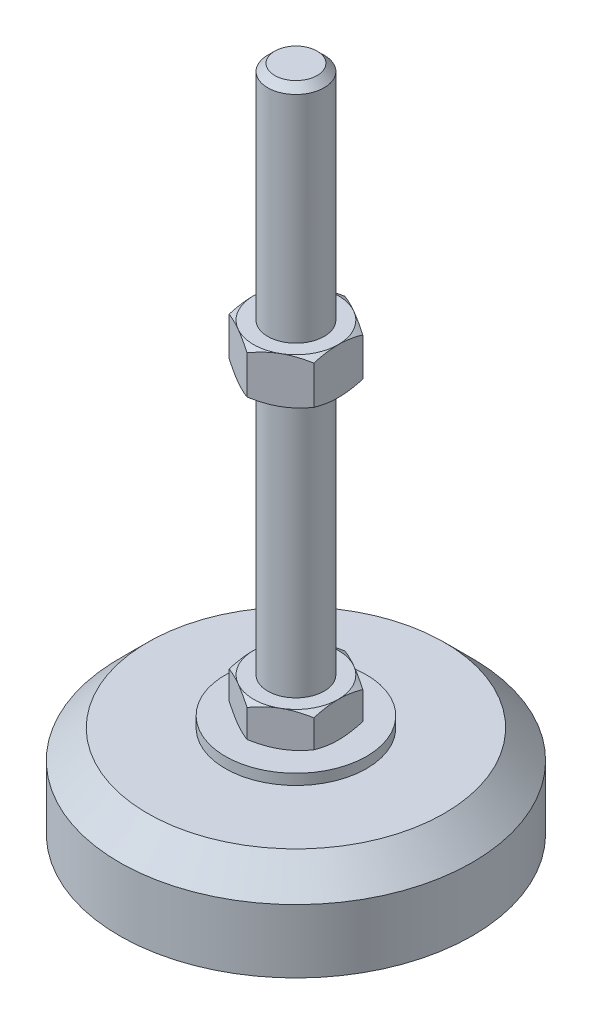
SolidWorks part; units mm, degrees
ref_plane "Спереди" through (0, 0, 0) normal (0, 0, 1) x (1, 0, 0)
ref_plane "Сверху" through (0, 0, 0) normal (0, 1, 0) x (1, 0, 0)
ref_plane "Справа" through (0, 0, 0) normal (1, 0, 0) x (0, 0, -1)
sketch "Эскиз1" plane through (0, 0, 0) normal (0, 0, 1) x (1, 0, 0)
  line L0 (0, 0) -> (-50, 0)
  line L3 (-50, 0) -> (-50, 18)
  line L5 (-20, 29) -> (-8, 29)
  line L12 (-8, 39) -> (-8, 187)
  line L13 (-8, 187) -> (-6, 189)
  line L14 (-6, 189) -> (0, 189)
  line L15 (0, 189) -> (0, 0) construction
  line L16 (-8, 29) -> (0, 29) construction
  line L17 (0, 0) -> (0, 189)
  line L18 (0, 0) -> (0, -7.9595) construction
  line L19 (-8, 39) -> (-8, 29)
  line L20 (-20, 29) -> (-20, 26)
  line L21 (-20, 26) -> (-42, 26)
  line L22 (-42, 26) -> (-50, 18)
  point P8 (-8, 113)
  point P23 (-14, 29)
  dimension "D1" = 16
  dimension "D2" = 29
  dimension "D3" = 10
  dimension "D4" = 100
  dimension "D5" = 8
  dimension "D6" = 2
  dimension "D7" = 45
  dimension "D8" = 40
  dimension "D10" = 150
  dimension "D11" = 18
  dimension "D12" = 45
  dimension "D13" = 3
revolve "Повернуть1" add sketch "Эскиз1" angle 360 about L17
sketch "Эскиз2" plane through (0, 29, 0) normal (0, 1, 0) x (1, 0, 0)
  line L1 (0, 13.8564) -> (-12, 6.9282)
  line L2 (-12, 6.9282) -> (-12, -6.9282)
  line L3 (-12, -6.9282) -> (0, -13.8564)
  line L4 (0, -13.8564) -> (12, -6.9282)
  line L5 (12, -6.9282) -> (12, 6.9282)
  line L6 (12, 6.9282) -> (0, 13.8564)
  circle A0 centre (0, 0) radius 12 construction
  dimension "D1" = 24
extrude "Бобышка-Вытянуть1" add sketch "Эскиз2" along normal up to vertex (10 mm away) up to point (-8, 39, 0)
ref_plane "Плоскость1" through (0, 113, 0) normal (0, 1, 0) x (1, 0, 0)
sketch "Эскиз3" plane through (0, 113, 0) normal (0, 1, 0) x (1, 0, 0)
  line L6 (12, 6.9282) -> (0, 13.8564)
  line L7 (0, 13.8564) -> (-12, 6.9282)
  line L8 (-12, 6.9282) -> (-12, -6.9282)
  line L9 (-12, -6.9282) -> (0, -13.8564)
  line L10 (0, -13.8564) -> (12, -6.9282)
  line L11 (12, -6.9282) -> (12, 6.9282)
  line L12 (12, 6.9282) -> (0, 13.8564)
  line L13 (0, 13.8564) -> (-12, 6.9282)
  line L14 (-12, 6.9282) -> (-12, -6.9282)
  line L15 (-12, -6.9282) -> (0, -13.8564)
  line L16 (0, -13.8564) -> (12, -6.9282)
  line L17 (12, -6.9282) -> (12, 6.9282)
  dimension "D1" = 0
extrude "Бобышка-Вытянуть2" add sketch "Эскиз3" along normal blind 13
sketch "Эскиз4" plane through (0, 0, 0) normal (0, 0, 1) x (1, 0, 0)
  line L0 (-12, 126) -> (-23.2583, 119.5)
  line L1 (-23.2583, 119.5) -> (-23.2583, 126)
  line L2 (-23.2583, 126) -> (-12, 126)
  line L3 (-23.2583, 119.5) -> (-12, 113)
  line L4 (50, 113) -> (-50, 113) construction
  line L5 (-12, 113) -> (-23.2583, 113)
  line L6 (-23.2583, 113) -> (-23.2583, 119.5)
  line L7 (-12, 126) -> (-12, 113) construction
  line L8 (-12, 39) -> (-20.6603, 39)
  line L9 (-20.6603, 39) -> (-20.6603, 34)
  line L10 (-20.6603, 34) -> (-12, 39)
  line L11 (-12, 29) -> (-20.6603, 34)
  line L12 (-20.6603, 34) -> (-20.6603, 29)
  line L13 (-20.6603, 29) -> (-12, 29)
  line L14 (0, 189) -> (0, 96.3793) construction
  dimension "D1" = 30
  dimension "D2" = 30
revolve "Вырез-Повернуть2" cut sketch "Эскиз4" angle 360 about L14
